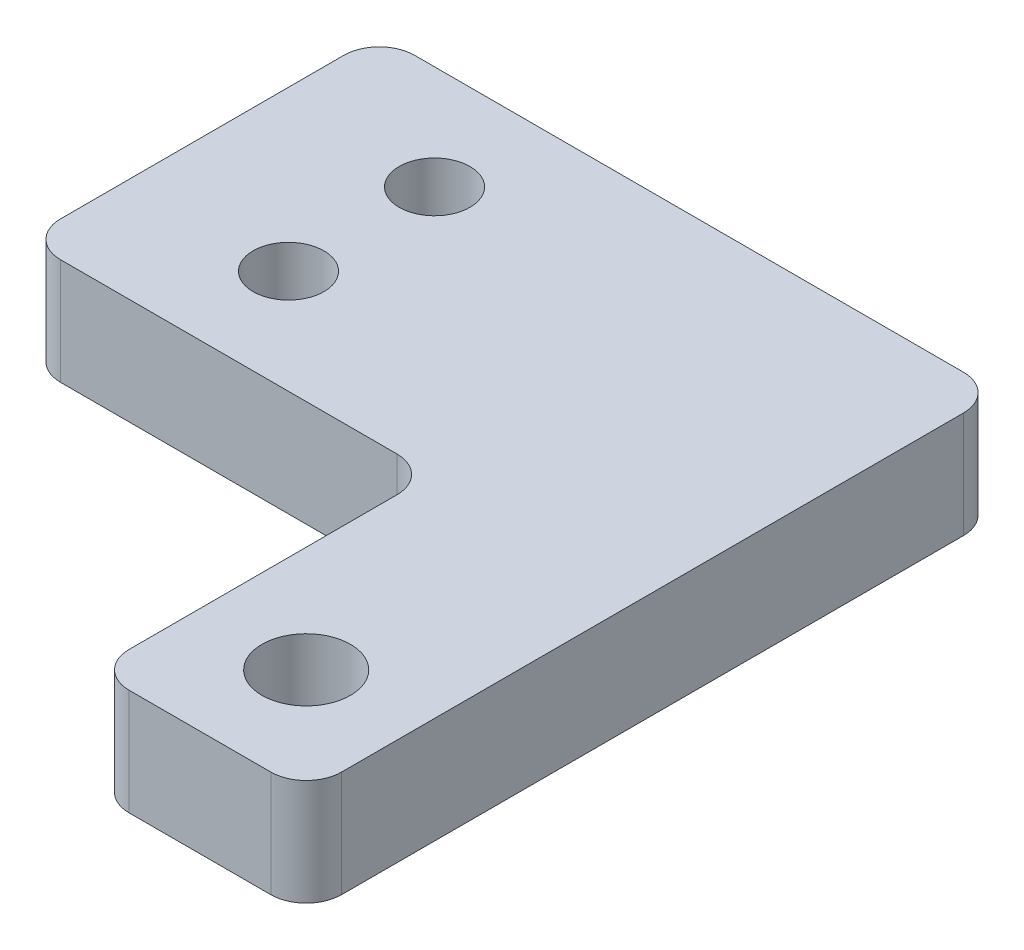
SolidWorks part; units mm, degrees
ref_plane "Front Plane" through (0, 0, 0) normal (0, 0, 1) x (1, 0, 0)
ref_plane "Top Plane" through (0, 0, 0) normal (0, 1, 0) x (1, 0, 0)
ref_plane "Right Plane" through (0, 0, 0) normal (1, 0, 0) x (0, 0, -1)
sketch "Sketch1" plane through (0, 0, 0) normal (0, 1, 0) x (1, 0, 0)
  line L0 (-9, 14.125) -> (-9, -5.875)
  line L1 (-9, -5.875) -> (14, -5.875)
  line L2 (14, -5.875) -> (14, -25)
  line L3 (14, -25) -> (26, -25)
  line L4 (26, -25) -> (26, 14.125)
  line L5 (26, 14.125) -> (-9, 14.125)
  line L6 (0, 8.25) -> (0, 0) construction
  line L7 (0, 4.125) -> (26, 4.125) construction
  circle A0 centre (0, 8.25) radius 2
  circle A1 centre (0, 0) radius 2
  circle A2 centre (20, -19) radius 2.5
  point P13 (0, 6.25)
  point P14 (0, 2)
  point P15 (0, 4.125)
  point P16 (-9, 4.125)
  point P18 (0, 0)
  point P21 (0, 0)
  point P22 (0, 0)
  dimension "D1" = 4
  dimension "D5" = 5
  dimension "D2" = 4.25
  dimension "D3" = 19
  dimension "D4" = 26
  dimension "D6" = 35
  dimension "D7" = 20
  dimension "D8" = 20
  dimension "D9" = 6
  dimension "D10" = 6
extrude "Boss-Extrude1" add sketch "Sketch1" along normal blind 6
fillet "Fillet1" radius 2 6 edges at (14, 3, 25) (26, 3, 25) (26, 3, -14.125) (-9, 3, -14.125) (-9, 3, 5.875) (14, 3, 5.875)
